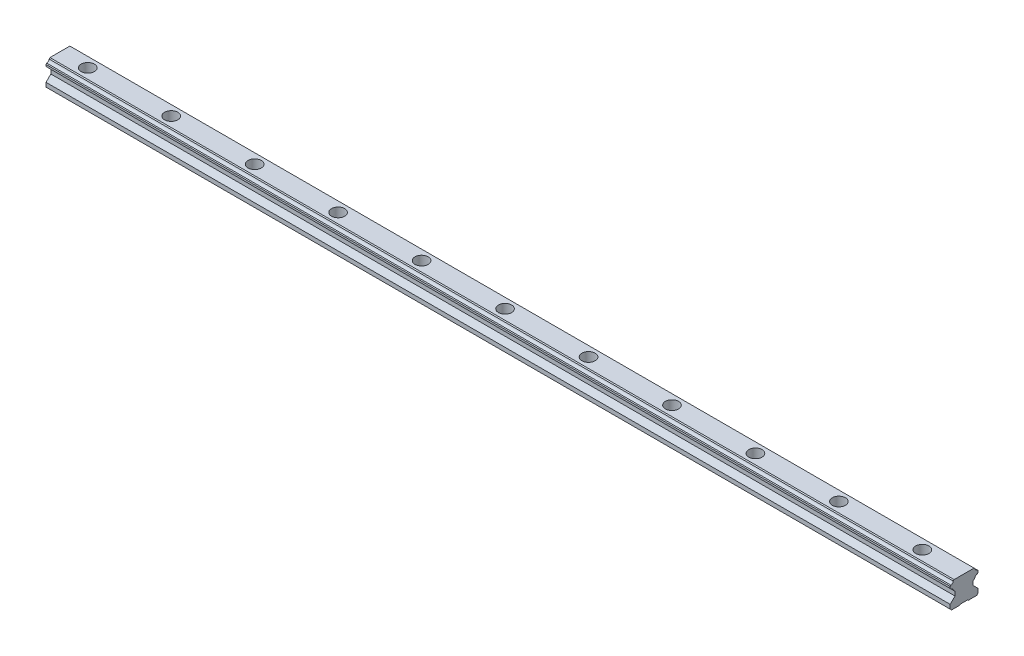
SolidWorks part; units mm, degrees
ref_plane "Front Plane" through (0, 0, 0) normal (0, 0, 1) x (1, 0, 0)
ref_plane "Top Plane" through (0, 0, 0) normal (0, 1, 0) x (1, 0, 0)
ref_plane "Right Plane" through (0, 0, 0) normal (1, 0, 0) x (0, 0, -1)
ref_plane "Plane1" through (-20, 0, 0) normal (1, 0, 0) x (0, 0, -1)
sketch "Sketch1" plane through (-20, 0, 0) normal (1, 0, 0) x (0, 0, -1)
  line L0 (-10, 4.0001) -> (-10, 1)
  line L1 (-10, 1) -> (-9, 0)
  line L2 (-9, 0) -> (-3, 0)
  line L3 (-3, 0) -> (-2.5, 0.5)
  line L4 (-2.5, 0.5) -> (2.5, 0.5)
  line L5 (2.5, 0.5) -> (3, 0)
  line L6 (3, 0) -> (9, 0)
  line L7 (9, 0) -> (10, 1)
  line L8 (10, 1) -> (10, 4.0001)
  line L9 (10, 4.0001) -> (6.55, 7.45)
  line L10 (6.55, 7.45) -> (6.55, 10.3792)
  line L11 (6.55, 10.3792) -> (7.7659, 11.5951)
  line L12 (9.4852, 13.3144) -> (10, 13.8292)
  line L13 (10, 13.8292) -> (10, 15.16)
  line L14 (10, 15.16) -> (9.4727, 15.6874)
  line L15 (7.7679, 17.3921) -> (7.16, 18)
  line L16 (7.16, 18) -> (-7.16, 18)
  line L17 (-7.16, 18) -> (-7.7679, 17.3921)
  line L18 (-9.4727, 15.6874) -> (-10, 15.16)
  line L19 (-10, 15.16) -> (-10, 13.8292)
  line L20 (-10, 13.8292) -> (-9.4852, 13.3144)
  line L21 (-7.7659, 11.5951) -> (-6.55, 10.3792)
  line L22 (-6.55, 10.3792) -> (-6.55, 7.45)
  line L23 (-6.55, 7.45) -> (-10, 4.0001)
  arc A0 (7.7659, 11.5951) -> (9.4852, 13.3144) centre (9.8015, 11.2788) cw
  arc A1 (9.4727, 15.6874) -> (7.7679, 17.3921) centre (9.8015, 17.7209) cw
  arc A2 (-7.7679, 17.3921) -> (-9.4727, 15.6874) centre (-9.8015, 17.7209) cw
  arc A3 (-9.4852, 13.3144) -> (-7.7659, 11.5951) centre (-9.8015, 11.2788) cw
extrude "Boss-Extrude1" add sketch "Sketch1" along normal blind 650
ref_plane "Plane2" through (0, 0, 0) normal (0, 0, 1) x (1, 0, 0)
sketch "Sketch2" plane through (0, 0, 0) normal (0, 0, 1) x (1, 0, 0)
  line L0 (0, 18) -> (4.75, 18)
  line L1 (4.75, 18) -> (4.75, 9.5)
  line L2 (4.75, 9.5) -> (3, 9.5)
  line L3 (3, 9.5) -> (3, 0)
  line L4 (3, 0) -> (0, 0)
  line L5 (0, 0) -> (0, 18)
  line L6 (0, 0) -> (0, 18) construction
revolve "Cut-Revolve1" cut sketch "Sketch2" angle 360 about L6
ref_plane "Plane3" through (0, 0, 0) normal (0, 0, 1) x (1, 0, 0)
sketch "Sketch3" plane through (0, 0, 0) normal (0, 0, 1) x (1, 0, 0)
  line L0 (60, 18) -> (64.75, 18)
  line L1 (64.75, 18) -> (64.75, 9.5)
  line L2 (64.75, 9.5) -> (63, 9.5)
  line L3 (63, 9.5) -> (63, 0)
  line L4 (63, 0) -> (60, 0)
  line L5 (60, 0) -> (60, 18)
  line L6 (60, 0) -> (60, 18) construction
  dimension "D1" = 4.75
  dimension "D2" = 8.5
  dimension "D3" = 3
  dimension "D4" = 9.5
revolve "Cut-Revolve2" cut sketch "Sketch3" angle 360 about L6
ref_plane "Plane4" through (0, 0, 0) normal (0, 0, 1) x (1, 0, 0)
sketch "Sketch4" plane through (0, 0, 0) normal (0, 0, 1) x (1, 0, 0)
  line L0 (120, 18) -> (124.75, 18)
  line L1 (124.75, 18) -> (124.75, 9.5)
  line L2 (124.75, 9.5) -> (123, 9.5)
  line L3 (123, 9.5) -> (123, 0)
  line L4 (123, 0) -> (120, 0)
  line L5 (120, 0) -> (120, 18)
  line L6 (120, 0) -> (120, 18) construction
revolve "Cut-Revolve3" cut sketch "Sketch4" angle 360 about L6
pattern_linear "LPattern1" count 9 spacing 60 along (1, 0, 0) of "Cut-Revolve3"
